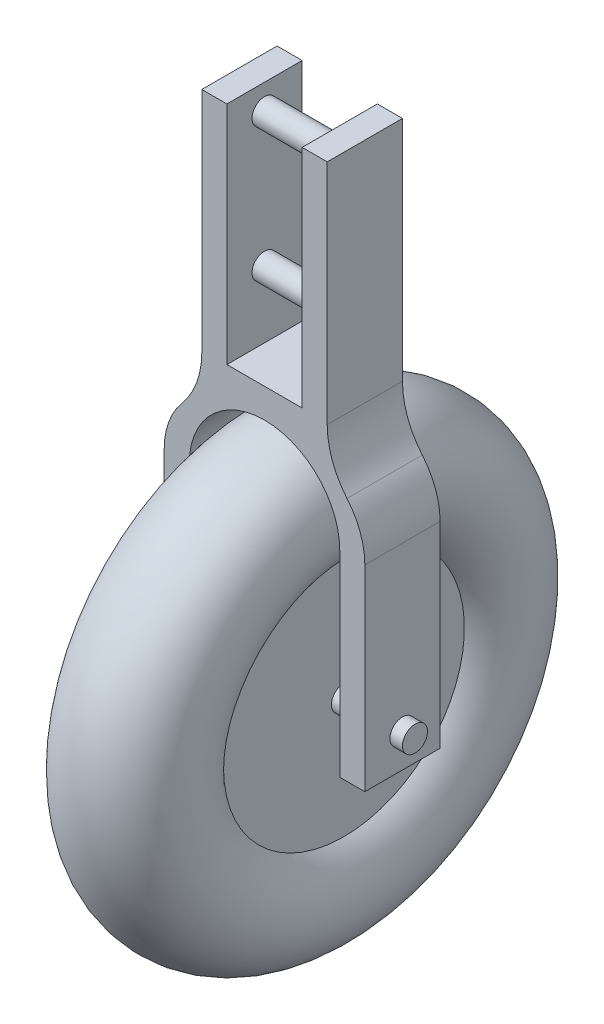
SolidWorks part; units mm, degrees
material "1060 Alloy"
ref_plane "Front" through (0, 0, 0) normal (0, 0, 1) x (1, 0, 0)
ref_plane "Top" through (0, 0, 0) normal (0, 1, 0) x (1, 0, 0)
ref_plane "Right" through (0, 0, 0) normal (1, 0, 0) x (0, 0, -1)
sketch "Sketch1" plane through (0, 0, 0) normal (0, 0, 1) x (1, 0, 0)
  line L0 (0, 0) -> (0, 27) construction
  line L1 (-7.5, 27) -> (-4.5, 27)
  line L2 (-4.5, 27) -> (-4.5, 0)
  line L3 (-4.5, 0) -> (4.5, 0)
  line L4 (-7.5, 27) -> (-7.5, -0.222)
  line L5 (-12, -36) -> (-12, -12.5)
  line L6 (-12, -36) -> (-9, -36)
  line L7 (-9, -36) -> (-9, -12.5)
  line L8 (12, -36) -> (9, -36)
  line L9 (12, -36) -> (12, -12.5)
  line L10 (9, -36) -> (9, -12.5)
  line L11 (4.5, 27) -> (4.5, 0)
  line L12 (7.5, 27) -> (7.5, -0.222)
  line L13 (7.5, 27) -> (4.5, 27)
  arc A0 (-9, -12.5) -> (0, -3.5) centre (0, -12.5) cw
  arc A1 (-12, -12.5) -> (-9.8684, -6.6841) centre (-3, -12.5) cw
  arc A2 (-7.5, -0.222) -> (-9.8684, -6.6841) centre (-17.5, -0.222) cw
  arc A3 (9, -12.5) -> (0, -3.5) centre (0, -12.5) ccw
  arc A4 (12, -12.5) -> (9.8684, -6.6841) centre (3, -12.5) ccw
  arc A5 (7.5, -0.222) -> (9.8684, -6.6841) centre (17.5, -0.222) ccw
  dimension "D7" = 10
  dimension "D1" = 3
  dimension "D2" = 27
  dimension "D3" = 9
  dimension "D4" = 3.5
  dimension "D5" = 36
  dimension "D6" = 3
  dimension "D8" = 18
extrude "Boss-Extrude1" add sketch "Sketch1" along normal blind 9
sketch "Sketch2" plane through (7.5, 0, 0) normal (1, 0, 0) x (0, 0, -1)
  line L0 (-9, 27) -> (0, 27) construction
  circle A0 centre (-4.5, 24) radius 1.5
  circle A1 centre (-4.5, 8) radius 1.5
  point P8 (-4.5, 27)
  dimension "D1" = 3
  dimension "D2" = 3
  dimension "D3" = 16
ref_plane "Plane1" through (0, 0, 4.5) normal (0, 0, 1) x (1, 0, 0)
sketch "Sketch3" plane through (0, 0, 0) normal (1, 0, 0) x (0, 0, -1)
  line L0 (-9, -36) -> (0, -36) construction
  circle A0 centre (-4.5, -32) radius 1.5
  point P5 (-4.5, -36)
  dimension "D1" = 3
  dimension "D2" = 4
extrude "Boss-Extrude2" add sketch "Sketch3" along normal mid plane 27
sketch "Sketch4" plane through (0, 0, 4.5) normal (0, 0, 1) x (1, 0, 0)
  line L0 (0, -33.5) -> (0, -25.0754) construction
  line L1 (-9, -33.5) -> (9, -33.5) construction
  line L2 (-5.4483, -4.5) -> (5.9552, -4.5) construction
  line L3 (-13.5, -32) -> (13.5, -32) construction
  line L4 (-13.5, -30.5) -> (-13.5, -33.5) construction
  line L5 (13.5, -33.5) -> (13.5, -30.5) construction
  line L7 (-5, -32) -> (5, -32)
  line L8 (-5, -32) -> (-5, -17.5902)
  line L10 (5, -32) -> (5, -17.5902)
  arc A0 (5, -17.5902) -> (-5, -17.5902) centre (0, -12) ccw
  point P19 (0, -32)
  dimension "D1" = 27.5
  dimension "D2" = 15
  dimension "D3" = 10
revolve "Revolve1" add sketch "Sketch4" angle 360 about L3
extrude "Boss-Extrude3" add sketch "Sketch2" against normal up to surface (15 mm away) up to face at (-7.5, 13.389, 4.5)
